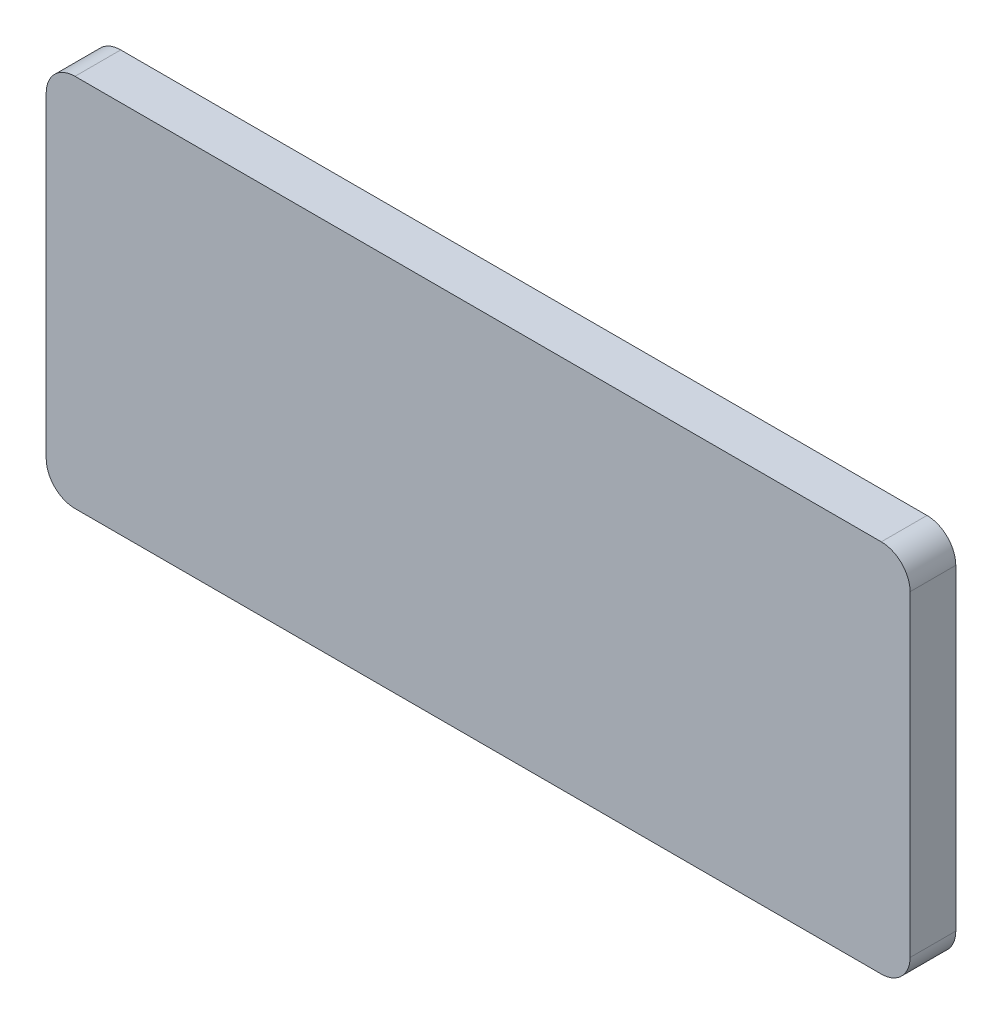
SolidWorks part; units mm, degrees
ref_plane "Front Plane" through (0, 0, 0) normal (0, 0, 1) x (1, 0, 0)
ref_plane "Top Plane" through (0, 0, 0) normal (0, 1, 0) x (1, 0, 0)
ref_plane "Right Plane" through (0, 0, 0) normal (1, 0, 0) x (0, 0, -1)
sketch "Sketch1" plane through (0, 0, 0) normal (0, 0, 1) x (1, 0, 0)
  line L1 (0, 0) -> (-60, 0)
  line L2 (0, 0) -> (0, 26)
  line L3 (0, 26) -> (-60, 26)
  line L4 (-60, 0) -> (-60, 26)
  dimension "D1" = 60
  dimension "D2" = 26
extrude "Boss-Extrude1" add sketch "Sketch1" along normal blind 3.175
fillet "Fillet1" radius 2
